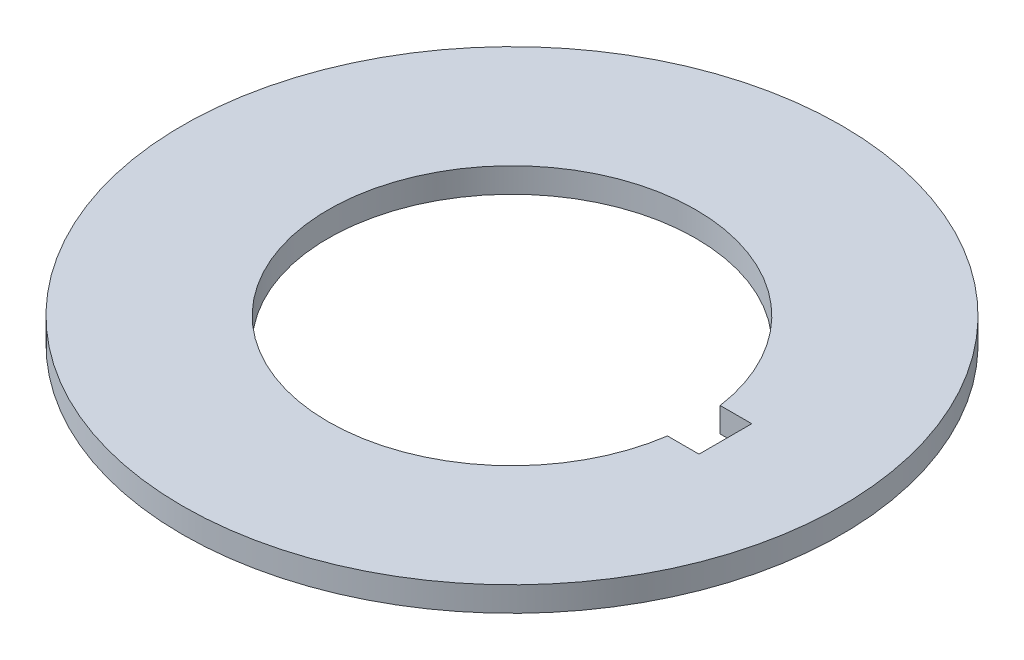
SolidWorks part; units mm, degrees
ref_plane "Front Plane" through (0, 0, 0) normal (0, 0, 1) x (1, 0, 0)
ref_plane "Top Plane" through (0, 0, 0) normal (0, 1, 0) x (1, 0, 0)
ref_plane "Right Plane" through (0, 0, 0) normal (1, 0, 0) x (0, 0, -1)
sketch "Sketch1" plane through (0, 0, 0) normal (0, 1, 0) x (1, 0, 0)
  line L0 (11.0346, 1.6) -> (12.95, 1.6)
  line L1 (12.95, 1.6) -> (12.95, -1.6)
  line L2 (12.95, -1.6) -> (11.0346, -1.6)
  arc A0 (11.0346, 1.6) -> (11.0346, -1.6) centre (0, 0) ccw
  circle A1 centre (0, 0) radius 20
  arc A2 (11.0346, -1.6) -> (11.0346, 1.6) centre (0, 0) ccw construction
  point P6 (12.95, 0)
  point P9 (-11.15, 0)
  dimension "D1" = 22.3
  dimension "D4" = 40
  dimension "D2" = 3.2
  dimension "D3" = 24.1
extrude "Boss-Extrude1" add sketch "Sketch1" along normal blind 1.5
